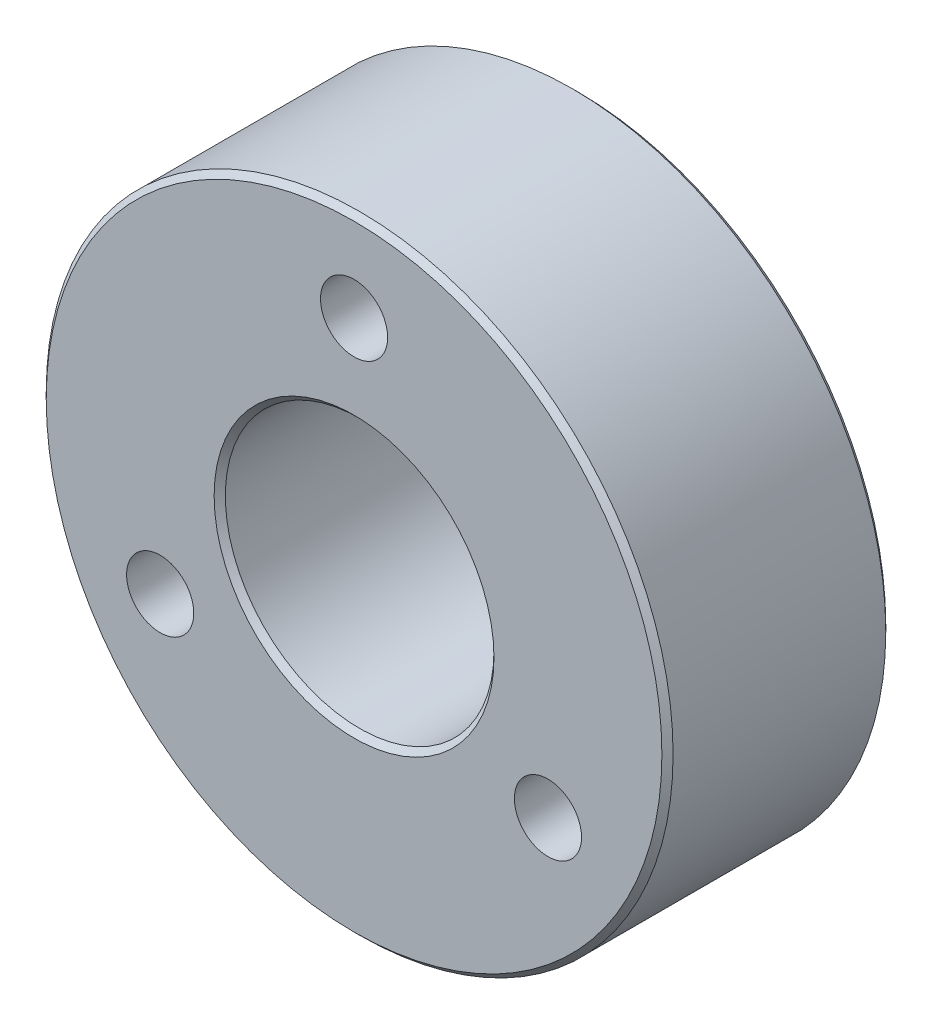
SolidWorks part; units mm, degrees
ref_plane "Front Plane" through (0, 0, 0) normal (0, 0, 1) x (1, 0, 0)
ref_plane "Top Plane" through (0, 0, 0) normal (0, 1, 0) x (1, 0, 0)
ref_plane "Right Plane" through (0, 0, 0) normal (1, 0, 0) x (0, 0, -1)
sketch "Sketch1" plane through (0, 0, 0) normal (0, 0, 1) x (1, 0, 0)
  circle A0 centre (0, 0) radius 6
  circle A1 centre (0, 0) radius 14
  circle A2 centre (0, 0) radius 10 construction
  circle A3 centre (0, 10) radius 1.5
  circle A4 centre (8.6603, -5) radius 1.5
  circle A5 centre (-8.6603, -5) radius 1.5
  dimension "D1" = 28
  dimension "D2" = 12
  dimension "D3" = 20
  dimension "D4" = 3
  dimension "D5" = 3
extrude "Boss-Extrude1" add sketch "Sketch1" along normal mid plane 10
chamfer "Chamfer1" distance 0.25 angle 45 4 edges at (14, 0, -5) (14, 0, 5) (6, 0, -5) (6, 0, 5)
